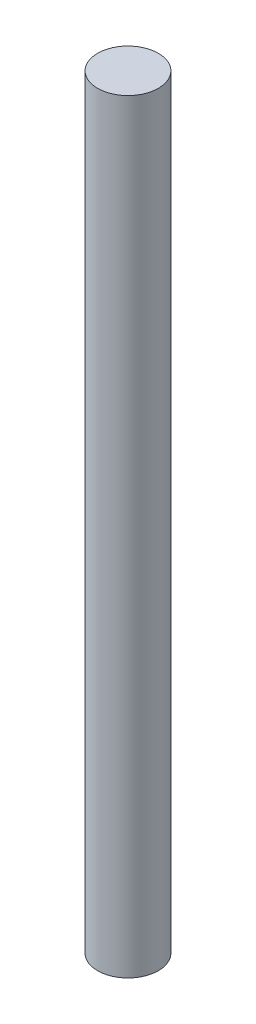
SolidWorks part; units mm, degrees
ref_plane "Front Plane" through (0, 0, 0) normal (0, 0, 1) x (1, 0, 0)
ref_plane "Top Plane" through (0, 0, 0) normal (0, 1, 0) x (1, 0, 0)
ref_plane "Right Plane" through (0, 0, 0) normal (1, 0, 0) x (0, 0, -1)
sketch "Sketch1" plane through (0, 0, 0) normal (0, 1, 0) x (1, 0, 0)
  circle A0 centre (0, 0) radius 0.762
extrude "Boss-Extrude1" add sketch "Sketch1" along normal blind 19.177
